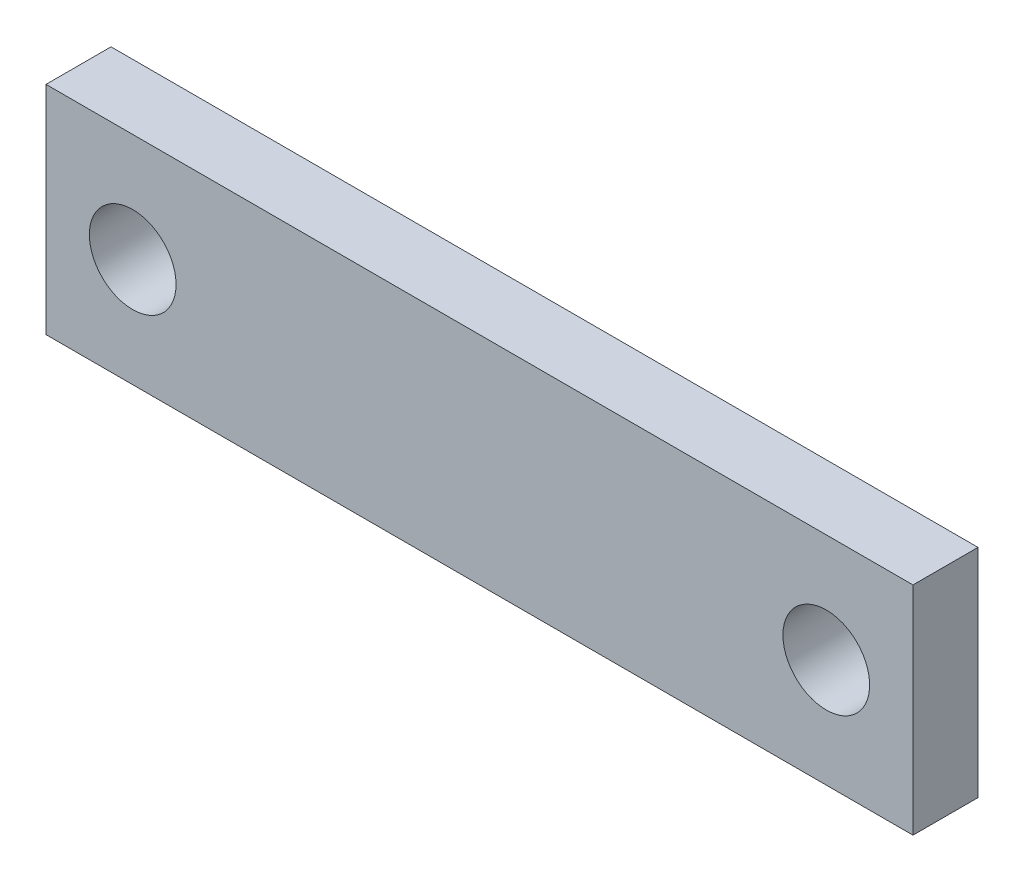
SolidWorks part; units mm, degrees
ref_plane "Front Plane" through (0, 0, 0) normal (0, 0, 1) x (1, 0, 0)
ref_plane "Top Plane" through (0, 0, 0) normal (0, 1, 0) x (1, 0, 0)
ref_plane "Right Plane" through (0, 0, 0) normal (1, 0, 0) x (0, 0, -1)
sketch "Sketch1" plane through (0, 0, 0) normal (0, 0, 1) x (1, 0, 0)
  line L0 (0, 2.5) -> (0, -2.5) construction
  line L1 (-10, 2.5) -> (10, 2.5)
  line L2 (-10, 2.5) -> (-10, -2.5)
  line L3 (-10, -2.5) -> (10, -2.5)
  line L4 (10, 2.5) -> (10, -2.5)
  line L5 (-10, 2.5) -> (10, -2.5) construction
  line L6 (-10, -2.5) -> (10, 2.5) construction
  circle A0 centre (-8, 0) radius 1
  circle A1 centre (8, 0) radius 1
  point P0 (0, 0)
  dimension "D3" = 2
  dimension "D4" = 2
  dimension "D1" = 20
  dimension "D2" = 5
extrude "Boss-Extrude1" add sketch "Sketch1" along normal blind 1.5
